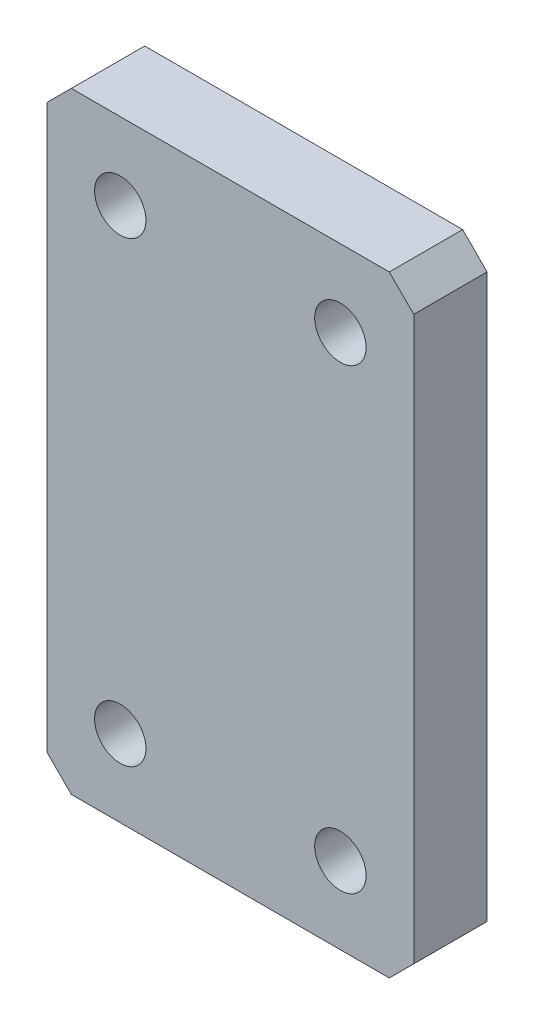
SolidWorks part; units mm, degrees
ref_plane "Front" through (0, 0, 0) normal (0, 0, 1) x (1, 0, 0)
ref_plane "Top" through (0, 0, 0) normal (0, 1, 0) x (1, 0, 0)
ref_plane "Right" through (0, 0, 0) normal (1, 0, 0) x (0, 0, -1)
sketch "Sketch1" plane through (0, 0, 0) normal (0, 0, 1) x (1, 0, 0)
  line L0 (-22.4943, 0) -> (72.9034, 0) construction
  line L1 (0, 25) -> (30, 25)
  line L2 (0, 25) -> (0, -25)
  line L3 (0, -25) -> (30, -25)
  line L4 (30, 25) -> (30, -25)
  dimension "D1" = 30
  dimension "D2" = 50
extrude "Boss-Extrude1" add sketch "Sketch1" along normal blind 6
hole_wizard "M5x0.8 Tapped Hole1" positions "Sketch3" profile "Sketch2" tap size "M5x0.8" standard "JIS" end condition through all
sketch "Sketch3" plane through (0, 0, 6) normal (0, 0, 1) x (1, 0, 0)
  line L0 (-3.6487, 0) -> (36.6786, 0) construction
  line L2 (0, 25) -> (0, -25) construction
  line L3 (30, -25) -> (30, 25) construction
  line L4 (30, 25) -> (0, 25) construction
  line L5 (0, -25) -> (30, -25) construction
  point P0 (6, 18.7)
  point P1 (6, -18.7)
  point P3 (24, -18.7)
  point P5 (24, 18.7)
  dimension "D1" = 37.4
  dimension "D2" = 18
  dimension "D3" = 6
  dimension "D4" = 6
  dimension "D5" = 6.3
  dimension "D6" = 6.3
sketch "Sketch2" plane through (6, 18.7, 6) normal (1, 0, 0) x (0, -1, 0)
  line L0 (0, 0) -> (0, 6)
  line L1 (0, 6) -> (2.1, 6)
  line L2 (2.1, 6) -> (2.1, 0)
  line L5 (2.1, 0) -> (0, 0)
  line L11 (0, -6.35) -> (0, 107.95) construction
  dimension "次ｻｰﾌｪｽまでのねじ下穴ﾄﾞﾘﾙ直径" = 4.2
  dimension "次ｻｰﾌｪｽまでのねじ下穴ﾄﾞﾘﾙの深さ" = 6
cosmetic thread "Hole Thread1" parameters "D2"=5
cosmetic thread "Hole Thread2" parameters "D2"=5
cosmetic thread "Hole Thread3" parameters "D2"=5
cosmetic thread "Hole Thread4" parameters "D2"=5
chamfer "Chamfer1" distance 2 angle 45 4 edges at (0, -25, 3) (30, -25, 3) (30, 25, 3) (0, 25, 3)
